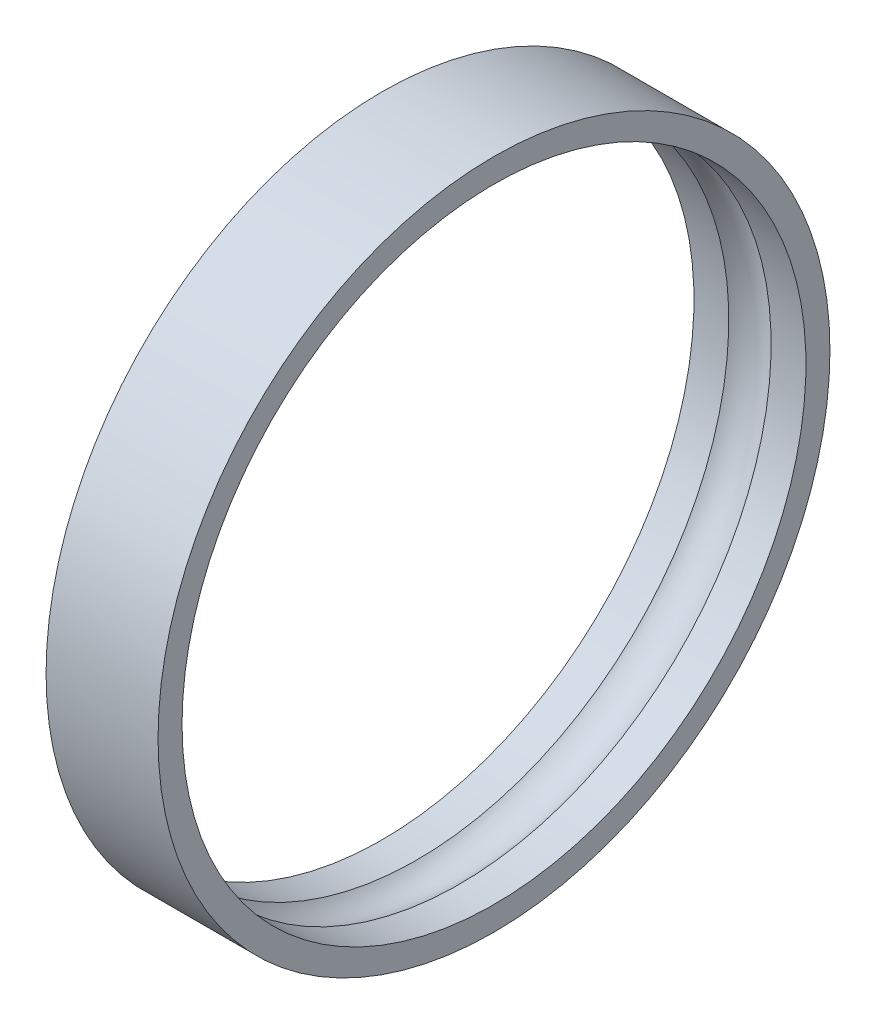
SolidWorks part; units mm, degrees
ref_plane "前视基准面" through (0, 0, 0) normal (0, 0, 1) x (1, 0, 0)
ref_plane "上视基准面" through (0, 0, 0) normal (0, 1, 0) x (1, 0, 0)
ref_plane "右视基准面" through (0, 0, 0) normal (1, 0, 0) x (0, 0, -1)
sketch "草图1" plane through (0, 0, 0) normal (0, 1, 0) x (1, 0, 0)
  line L0 (-3.5, -1.5) -> (-1.3229, -1.5)
  line L3 (-3.5, -3) -> (3.5, -3)
  line L5 (1.3229, -1.5) -> (3.5, -1.5)
  line L6 (0, -3) -> (0, 18) construction
  line L7 (0, 18) -> (31.9578, 18) construction
  line L10 (-3.5, -1.5) -> (-3.5, -3)
  line L14 (3.5, -1.5) -> (3.5, -3)
  arc A0 (-1.3229, -1.5) -> (1.3229, -1.5) centre (0, 0) ccw
  point P0 (0, 0)
  point P11 (0, -3)
  dimension "D4" = 4
  dimension "D1" = 7
  dimension "D2" = 21
  dimension "D3" = 1.5
revolve "旋转1" add sketch "草图1" angle 360 about L7
